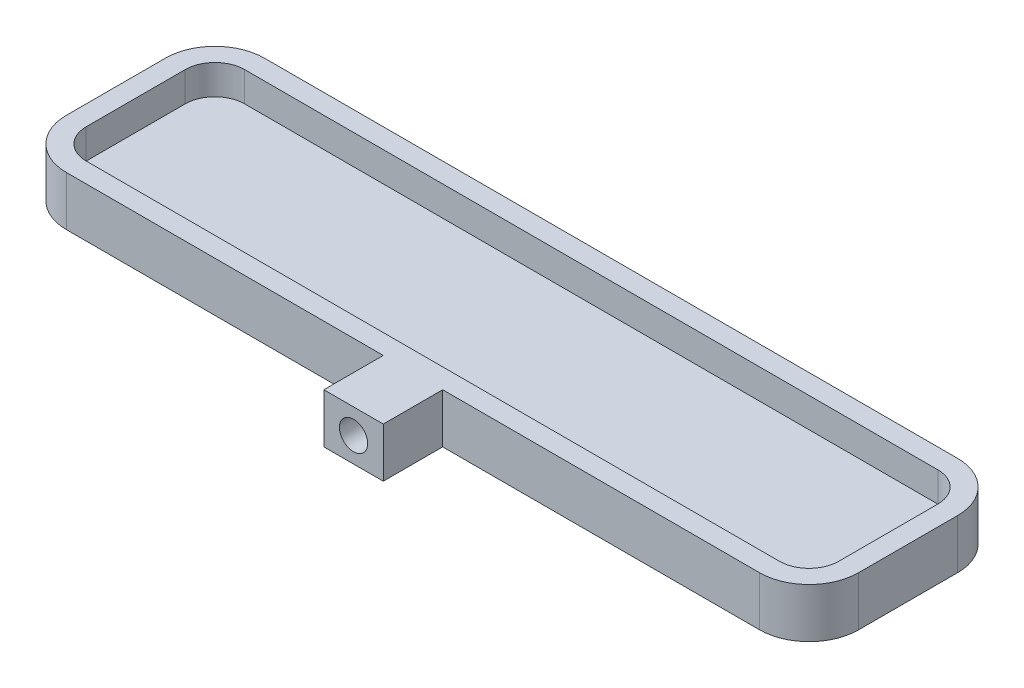
SolidWorks part; units mm, degrees
ref_plane "Front Plane" through (0, 0, 0) normal (0, 0, 1) x (1, 0, 0)
ref_plane "Top Plane" through (0, 0, 0) normal (0, 1, 0) x (1, 0, 0)
ref_plane "Right Plane" through (0, 0, 0) normal (1, 0, 0) x (0, 0, -1)
sketch "Sketch1" plane through (0, 0, 0) normal (0, 1, 0) x (1, 0, 0)
  line L1 (40, -10) -> (-40, -10)
  line L2 (40, -10) -> (40, 10)
  line L3 (40, 10) -> (-40, 10)
  line L4 (-40, -10) -> (-40, 10)
  line L5 (40, -10) -> (-40, 10) construction
  line L6 (40, 10) -> (-40, -10) construction
  point P0 (0, 0)
  dimension "D1" = 80
  dimension "D2" = 20
extrude "Boss-Extrude1" add sketch "Sketch1" along normal blind 5
fillet "Fillet1" radius 5 4 edges at (40, 2.5, 10) (40, 2.5, -10) (-40, 2.5, -10) (-40, 2.5, 10)
shell "Shell1" thickness 2
sketch "Sketch2" plane through (0, 0, 10) normal (0, 0, 1) x (1, 0, 0)
  line L0 (-35, 5) -> (35, 5) construction
  line L1 (3, 0) -> (-3, 0)
  line L2 (3, 0) -> (3, 5)
  line L3 (3, 5) -> (-3, 5)
  line L4 (-3, 0) -> (-3, 5)
  line L5 (3, 0) -> (-3, 5) construction
  line L6 (3, 5) -> (-3, 0) construction
  line L7 (-35, 0) -> (35, 0) construction
  line L8 (0, 0) -> (0, 2.066) construction
  point P0 (0, 2.5)
  dimension "D1" = 6
extrude "Boss-Extrude2" add sketch "Sketch2" along normal blind 6
sketch "Sketch3" plane through (0, 0, 16) normal (0, 0, 1) x (1, 0, 0)
  line L0 (0, 0) -> (0, 2.0871) construction
  line L1 (-3, 0) -> (3, 0) construction
  line L2 (3, 5) -> (-3, 5) construction
  circle A0 centre (0, 2.5) radius 1.425
  point P2 (0, 0)
  point P7 (0, 2.8618)
  dimension "D1" = 2.85
  dimension "D2" = 2.5
extrude "Cut-Extrude1" cut sketch "Sketch3" against normal blind 4
